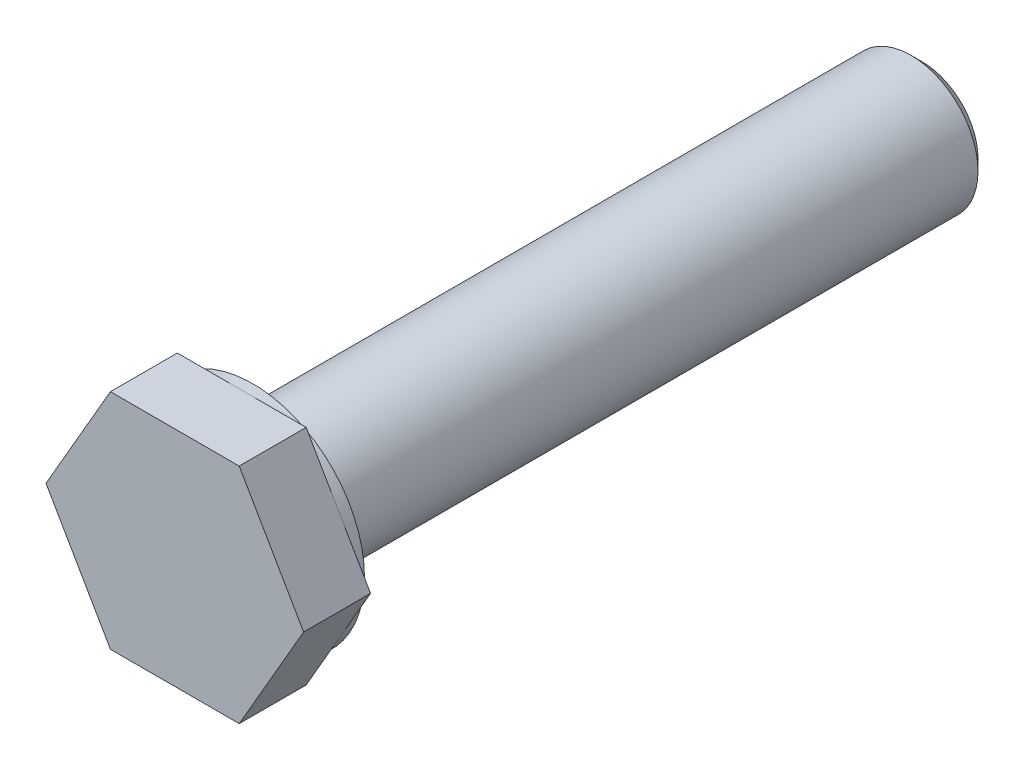
SolidWorks part; units mm, degrees
ref_plane "Front Plane" through (0, 0, 0) normal (0, 0, 1) x (1, 0, 0)
ref_plane "Top Plane" through (0, 0, 0) normal (0, 1, 0) x (1, 0, 0)
ref_plane "Right Plane" through (0, 0, 0) normal (1, 0, 0) x (0, 0, -1)
sketch "Sketch1" plane through (0, 0, 0) normal (0, 0, 1) x (1, 0, 0)
  circle A0 centre (0, 0) radius 3
  dimension "D1" = 6
extrude "Boss-Extrude1" add sketch "Sketch1" along normal blind 30
sketch "Sketch2" plane through (0, 0, 30) normal (0, 0, 1) x (1, 0, 0)
  circle A0 centre (0, 0) radius 5
  dimension "D1" = 10
extrude "Boss-Extrude2" add sketch "Sketch2" along normal blind 0.5
sketch "Sketch3" plane through (0, 0, 30.5) normal (0, 0, 1) x (1, 0, 0)
  line L1 (5.7735, 0) -> (2.8868, 5)
  line L2 (2.8868, 5) -> (-2.8868, 5)
  line L3 (-2.8868, 5) -> (-5.7735, 0)
  line L4 (-5.7735, 0) -> (-2.8868, -5)
  line L5 (-2.8868, -5) -> (2.8868, -5)
  line L6 (2.8868, -5) -> (5.7735, 0)
  circle A0 centre (0, 0) radius 5 construction
  circle A1 centre (0, 0) radius 5 construction
extrude "Boss-Extrude3" add sketch "Sketch3" along normal blind 3
chamfer "Chamfer1" distance 0.5 angle 45 1 edges at (3, 0, 0)
chamfer "Chamfer2" distance 0.25 angle 45 1 edges at (3, 0, 30)
